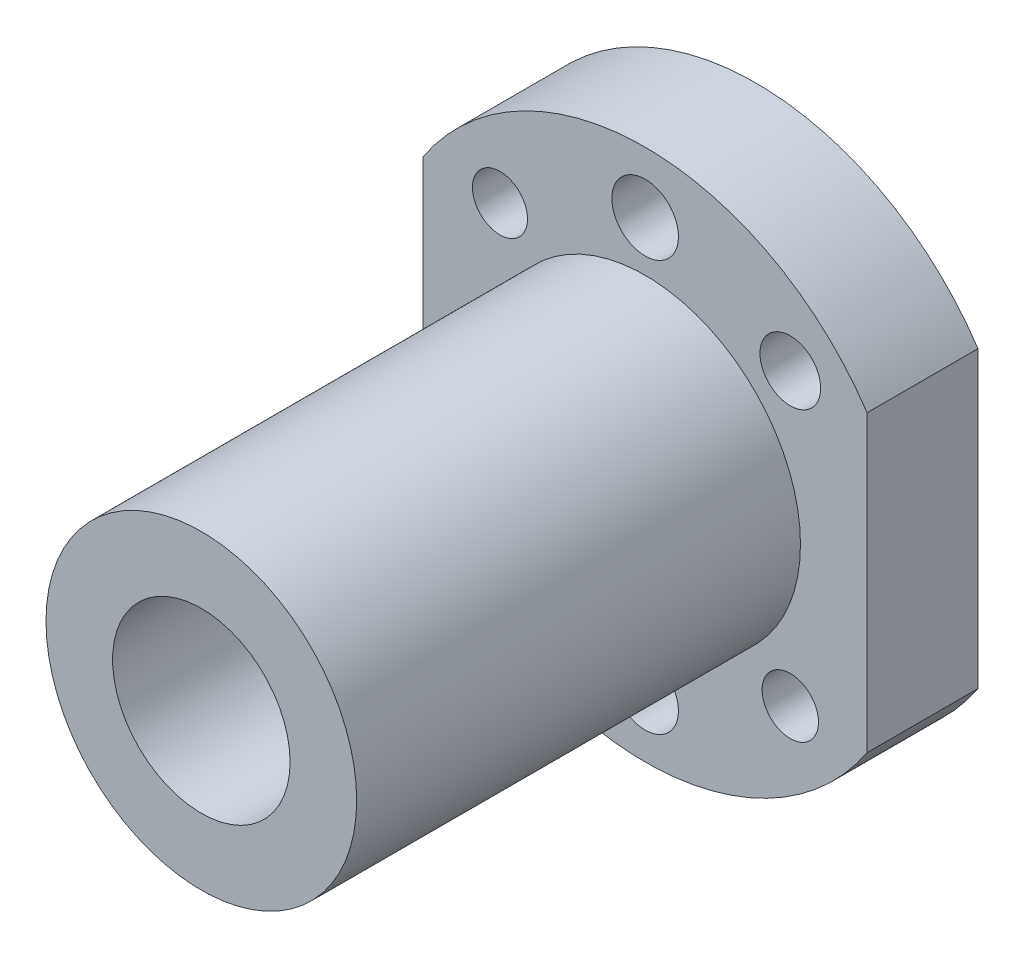
SolidWorks part; units mm, degrees
ref_plane "前视基准面" through (0, 0, 0) normal (0, 0, 1) x (1, 0, 0)
ref_plane "上视基准面" through (0, 0, 0) normal (0, 1, 0) x (1, 0, 0)
ref_plane "右视基准面" through (0, 0, 0) normal (1, 0, 0) x (0, 0, -1)
sketch "草图1" plane through (0, 0, 0) normal (0, 0, 1) x (1, 0, 0)
  circle A0 centre (0, 0) radius 24
  dimension "D1" = 48
extrude "凸台-拉伸1" add sketch "草图1" along normal blind 10
sketch "草图2" plane through (0, 0, 10) normal (0, 0, 1) x (1, 0, 0)
  circle A0 centre (0, 0) radius 14
  dimension "D1" = 28
extrude "凸台-拉伸2" add sketch "草图2" along normal blind 40
sketch "草图3" plane through (0, 0, 50) normal (0, 0, 1) x (1, 0, 0)
  circle A0 centre (0, 0) radius 8
  dimension "D1" = 16
extrude "切除-拉伸1" cut sketch "草图3" against normal blind 50
sketch "草图4" plane through (0, 0, 0) normal (0, 0, -1) x (-1, 0, 0)
  line L2 (-20, 13.2665) -> (-20, -13.2665)
  line L4 (20, 13.2665) -> (20, -13.2665)
  circle A0 centre (0, 0) radius 24 construction
  arc A1 (-20, 13.2665) -> (-20, -13.2665) centre (0, 0) ccw
  arc A2 (20, -13.2665) -> (20, 13.2665) centre (0, 0) ccw
  dimension "D2" = 20
  dimension "D3" = 20
extrude "切除-拉伸2" cut sketch "草图4" against normal blind 10
sketch "草图5" plane through (0, 0, 0) normal (0, 0, -1) x (-1, 0, 0)
  line L0 (0, 0) -> (0, 15.5031)
  line L1 (0, 24) -> (0, 21.5031)
  line L2 (0, 0) -> (-13.0837, -13.0837)
  line L3 (0, 0) -> (13.0837, -13.0837)
  line L4 (0, 0) -> (13.0837, 13.0837)
  line L5 (0, 0) -> (-13.0837, 13.0837)
  line L6 (0, 21.5031) -> (0, 24)
  line L7 (0, 15.5031) -> (0, -15.5031)
  arc A1 (20, 13.2665) -> (-20, 13.2665) centre (0, 0) ccw construction
  circle A2 centre (0, 18.5031) radius 3
  circle A3 centre (0, -18.5031) radius 3
  circle A4 centre (13.0837, 13.0837) radius 2.4813
  circle A5 centre (-13.0837, 13.0837) radius 2.7327
  circle A6 centre (-13.0837, -13.0837) radius 2.5428
  circle A7 centre (13.0837, -13.0837) radius 3.0824
  dimension "D1" = 6
  dimension "D2" = 6
  dimension "D3" = 45
  dimension "D4" = 45
  dimension "D5" = 45
  dimension "D6" = 45
extrude "切除-拉伸3" cut sketch "草图5" against normal blind 10
